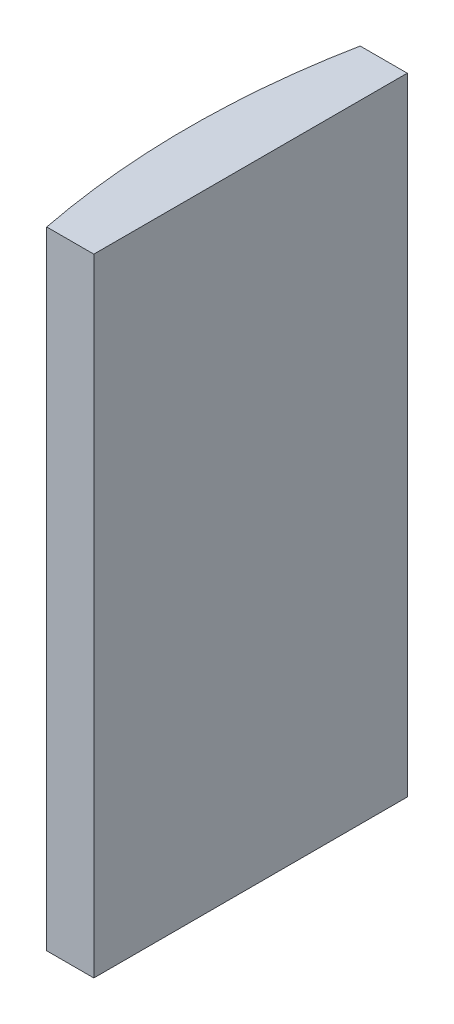
SolidWorks part; units mm, degrees
ref_plane "前视基准面" through (0, 0, 0) normal (0, 0, 1) x (1, 0, 0)
ref_plane "上视基准面" through (0, 0, 0) normal (0, 1, 0) x (1, 0, 0)
ref_plane "右视基准面" through (0, 0, 0) normal (1, 0, 0) x (0, 0, -1)
sketch "草图1" plane through (0, 0, 0) normal (0, 1, 0) x (1, 0, 0)
  line L0 (10.7432, 0) -> (-607.0701, 0) construction
  line L1 (-46.3481, 10) -> (-43.3448, 10)
  line L2 (-46.3481, -10) -> (-43.3448, -10)
  line L3 (-43.3448, 10) -> (-43.3448, -10)
  arc A0 (-46.3481, 10) -> (-46.3481, -10) centre (4.3552, 0) ccw
  point P19 (-47.3248, 0)
  point P20 (-43.3448, 0)
  dimension "D2" = 10
  dimension "D3" = 51.68
  dimension "D4" = 3.98
  dimension "D1" = 10
extrude "凸台-拉伸1" add sketch "草图1" along normal blind 40
